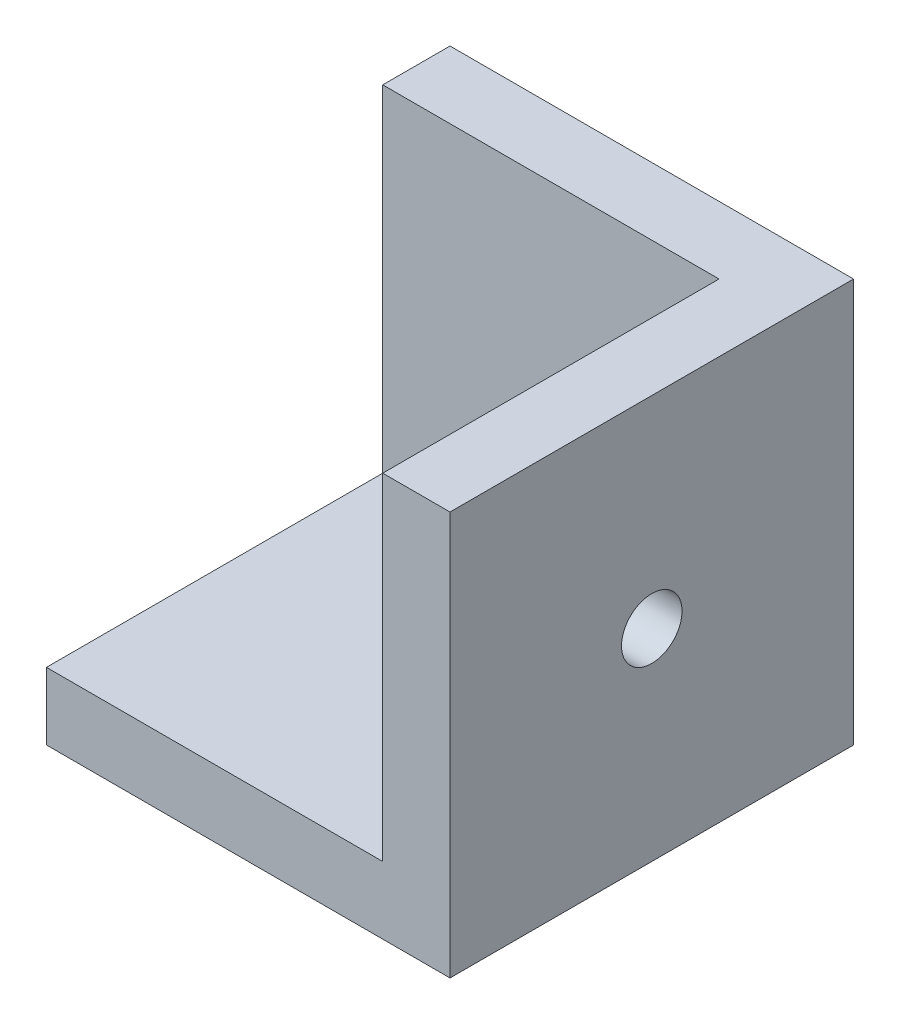
SolidWorks part; units mm, degrees
material "ABS"
ref_plane "Plano frontal" through (0, 0, 0) normal (0, 0, 1) x (1, 0, 0)
ref_plane "Plano superior" through (0, 0, 0) normal (0, 1, 0) x (1, 0, 0)
ref_plane "Plano direito" through (0, 0, 0) normal (1, 0, 0) x (0, 0, -1)
sketch "Esboço1" plane through (0, 0, 0) normal (0, 0, 1) x (1, 0, 0)
  line L9 (0, 0) -> (-30, 0)
  line L10 (0, 0) -> (0, 30)
  line L11 (0, 30) -> (-30, 30)
  line L12 (-30, 0) -> (-30, 30)
  dimension "D1" = 30
  dimension "D2" = 30
extrude "Ressalto-extrusão1" add sketch "Esboço1" along normal blind 30
sketch "Esboço3" plane through (0, 30, 0) normal (0, 1, 0) x (1, 0, 0)
  line L0 (0, -30) -> (0, 0) construction
  line L1 (-5, -5) -> (-30, -5)
  line L2 (-5, -5) -> (-5, -30)
  line L3 (-5, -30) -> (-30, -30)
  line L4 (-30, -5) -> (-30, -30)
  line L6 (0, 0) -> (-30, 0) construction
  dimension "D1" = 5
  dimension "D2" = 5
extrude "Corte-extrusão2" cut sketch "Esboço3" against normal blind 25
hole_wizard "Furo com folga de M41" positions "3DSketch1" profile "Esboço4" hole size "M4" standard "ISO" end condition through all
sketch3d "3DSketch1"
  line L0 (-5, 5, 5) -> (-5, 30, 5) construction
  line L1 (-5, 5, 30) -> (-5, 5, 5) construction
  line L2 (-5, 5, 5) -> (-30, 5, 5) construction
  point P0 (-5, 15, 15)
  point P7 (-15, 15, 5)
  point P9 (-15, 5, 15)
  dimension "D1" = 10
  dimension "D2" = 10
  dimension "D3" = 10
  dimension "D4" = 10
  dimension "D5" = 10
  dimension "D6" = 10
sketch "Esboço4" plane through (-5, 15, 15) normal (0, 1, 0) x (0, 0, 1)
  line L0 (0, 0) -> (0, 5)
  line L1 (0, 5) -> (2.25, 5)
  line L2 (2.25, 5) -> (2.25, 0)
  line L5 (2.25, 0) -> (0, 0)
  line L11 (0, -6.35) -> (0, 107.95) construction
  dimension "Thru Hole Dia." = 4.5
  dimension "Thru Hole Depth" = 5
